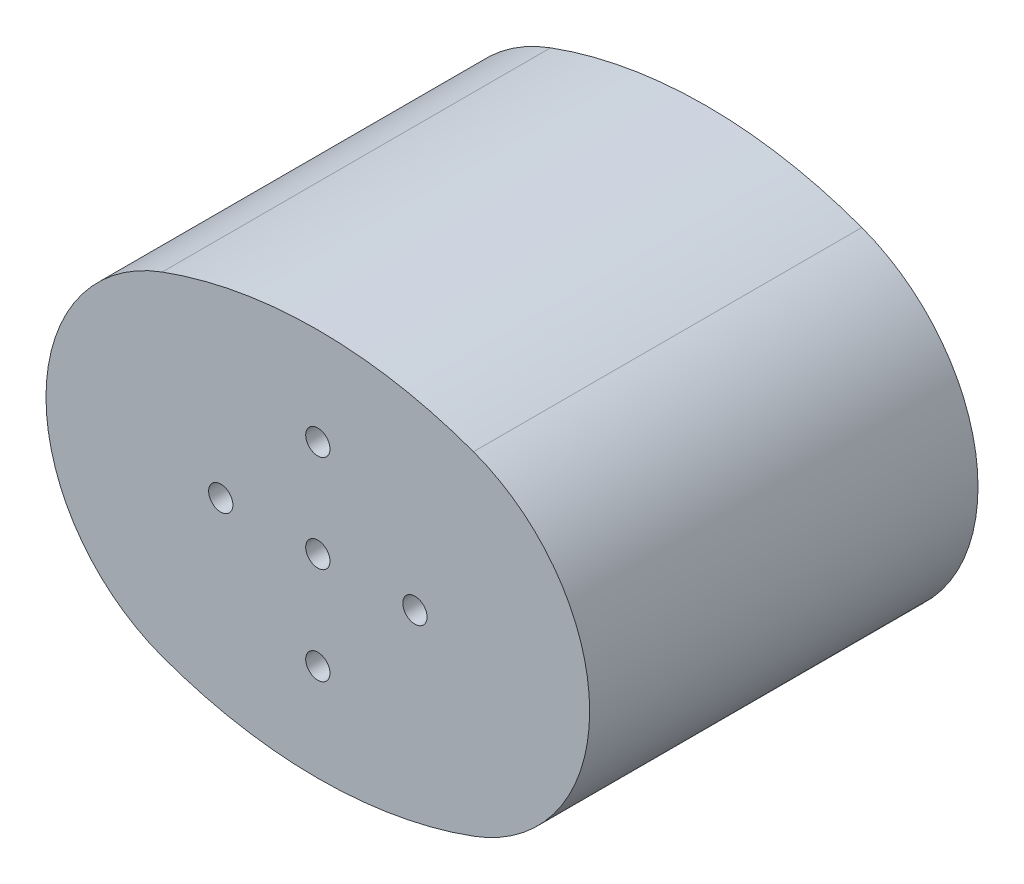
SolidWorks part; units mm, degrees
ref_plane "Front Plane" through (0, 0, 0) normal (0, 0, 1) x (1, 0, 0)
ref_plane "Top Plane" through (0, 0, 0) normal (0, 1, 0) x (1, 0, 0)
ref_plane "Right Plane" through (0, 0, 0) normal (1, 0, 0) x (0, 0, -1)
sketch "Sketch1" plane through (0, 0, 0) normal (0, 0, 1) x (1, 0, 0)
  line L0 (0, 0) -> (24856.2268, 0) construction
  line L1 (0, -3.4133) -> (0, 24852.8136) construction
  arc A0 (-16.0304, 17.1488) -> (-16.0304, -17.1488) centre (-9.7308, 0) ccw
  arc A2 (16.0304, -17.1488) -> (16.0304, 17.1488) centre (9.7308, 0) ccw
  arc A3 (16.0304, 17.1488) -> (-16.0304, 17.1488) centre (0, -26.489) ccw
  arc A4 (-16.0304, -17.1488) -> (16.0304, -17.1488) centre (0, 26.489) ccw
  point P2 (0, 0)
  point P6 (0, 20)
  point P13 (0, -20)
  point P14 (-28, 0)
  point P15 (28, 0)
  point P16 (22.7482, 16.4789)
  point P17 (0, 0)
  point P18 (22.5933, 13.1473)
  point P19 (16.0304, 17.1488)
  dimension "D4" = 56
  dimension "D5" = 40
extrude "Boss-Extrude1" add sketch "Sketch1" along normal blind 40
sketch "Sketch2" plane through (0, 0, 40) normal (0, 0, 1) x (1, 0, 0)
  line L0 (0, 0) -> (50000, 0) construction
  line L1 (0, 0) -> (0, 50000) construction
  circle A0 centre (0, 10) radius 1.25
  circle A4 centre (10, 0) radius 1.25
  circle A5 centre (0, -10) radius 1.25
  circle A6 centre (-10, 0) radius 1.25
  circle A7 centre (0, 0) radius 1.25
  point P16 (0, 0)
  dimension "D1" = 2.5
  dimension "D3" = 4
  dimension "D2" = 10
extrude "Cut-Extrude1" cut sketch "Sketch2" against normal through all
